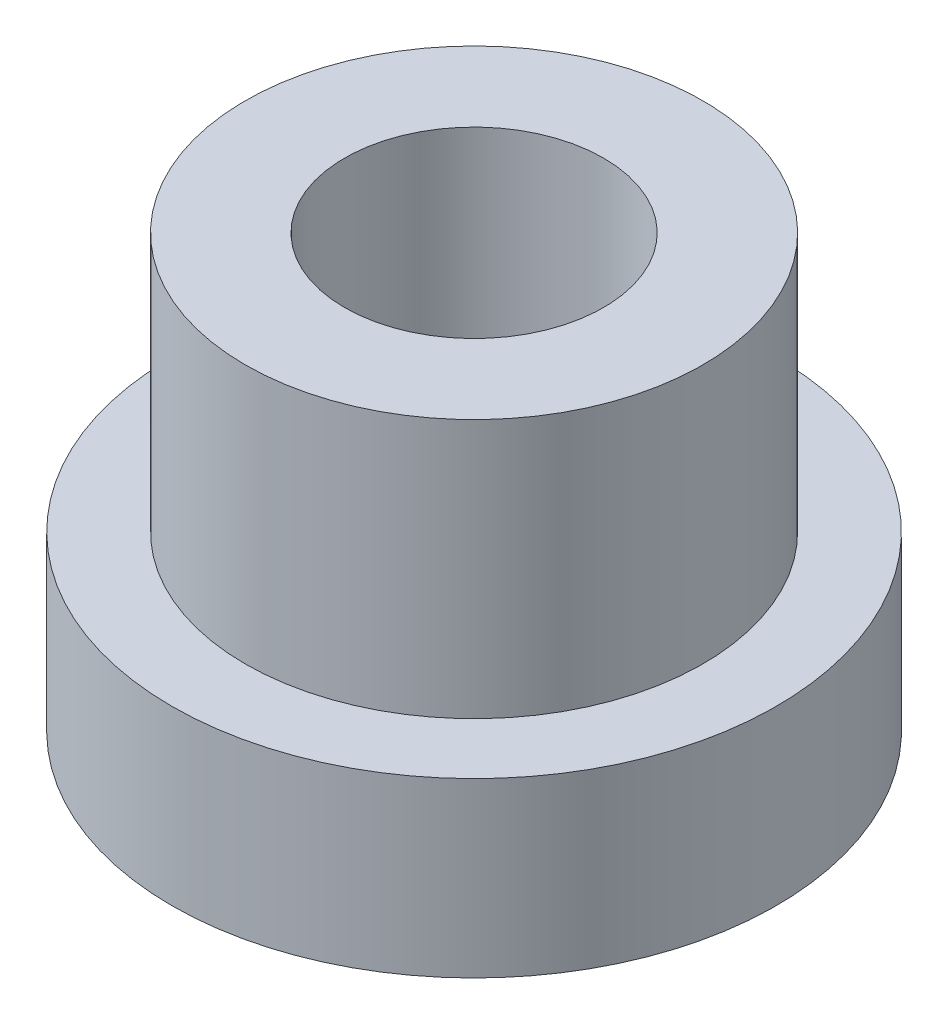
SolidWorks part; units mm, degrees
ref_plane "Plano frontal" through (0, 0, 0) normal (0, 0, 1) x (1, 0, 0)
ref_plane "Plano superior" through (0, 0, 0) normal (0, 1, 0) x (1, 0, 0)
ref_plane "Plano direito" through (0, 0, 0) normal (1, 0, 0) x (0, 0, -1)
sketch "Esboço1" plane through (0, 0, 0) normal (0, 1, 0) x (1, 0, 0)
  circle A0 centre (0, 0) radius 3.5
  dimension "D1" = 7
extrude "Ressalto-extrusão1" add sketch "Esboço1" along normal blind 2
sketch "Esboço2" plane through (0, 2, 0) normal (0, 1, 0) x (1, 0, 0)
  circle A0 centre (0, 0) radius 2.65
  dimension "D1" = 5.3
extrude "Ressalto-extrusão2" add sketch "Esboço2" along normal blind 3
sketch "Esboço3" plane through (0, 5, 0) normal (0, 1, 0) x (1, 0, 0)
  circle A0 centre (0, 0) radius 1.5
  dimension "D1" = 3
extrude "Corte-extrusão1" cut sketch "Esboço3" against normal blind 4
